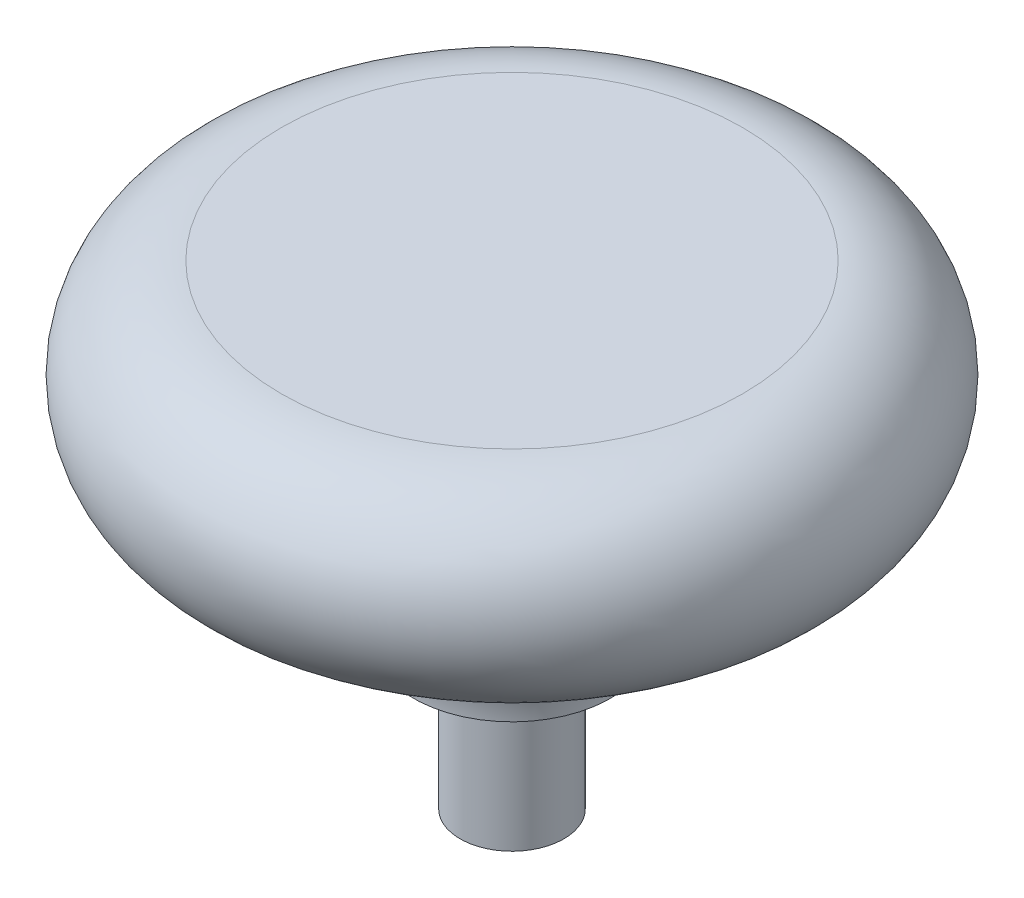
SolidWorks part; units mm, degrees
ref_plane "Front" through (0, 0, 0) normal (0, 0, 1) x (1, 0, 0)
ref_plane "Top" through (0, 0, 0) normal (0, 1, 0) x (-1, 0, 0)
ref_plane "Right" through (0, 0, 0) normal (1, 0, 0) x (0, 0, -1)
sketch "Sketch1" plane through (0, 0, 0) normal (0, 0, 1) x (1, 0, 0)
  line L0 (0, 0) -> (0, 36.2882) construction
  line L1 (0, 0) -> (0, 22.875)
  line L2 (0, 22.875) -> (11.1125, 22.875)
  line L4 (4.7625, 7) -> (2.5, 7)
  line L5 (2.5, 7) -> (2.5, 0)
  line L6 (2.5, 0) -> (0, 0)
  arc A0 (11.1125, 22.875) -> (11.1125, 13.35) centre (11.1125, 18.1125) cw
  arc A1 (11.1125, 13.35) -> (4.7625, 7) centre (11.1125, 7) ccw
  dimension "D5" = 6.35
  dimension "D6" = 4.7625
  dimension "D1" = 2.5
  dimension "D2" = 4.7625
  dimension "D3" = 7
  dimension "D4" = 15.875
revolve "Base-Revolve" add sketch "Sketch1" angle 360 about L0
